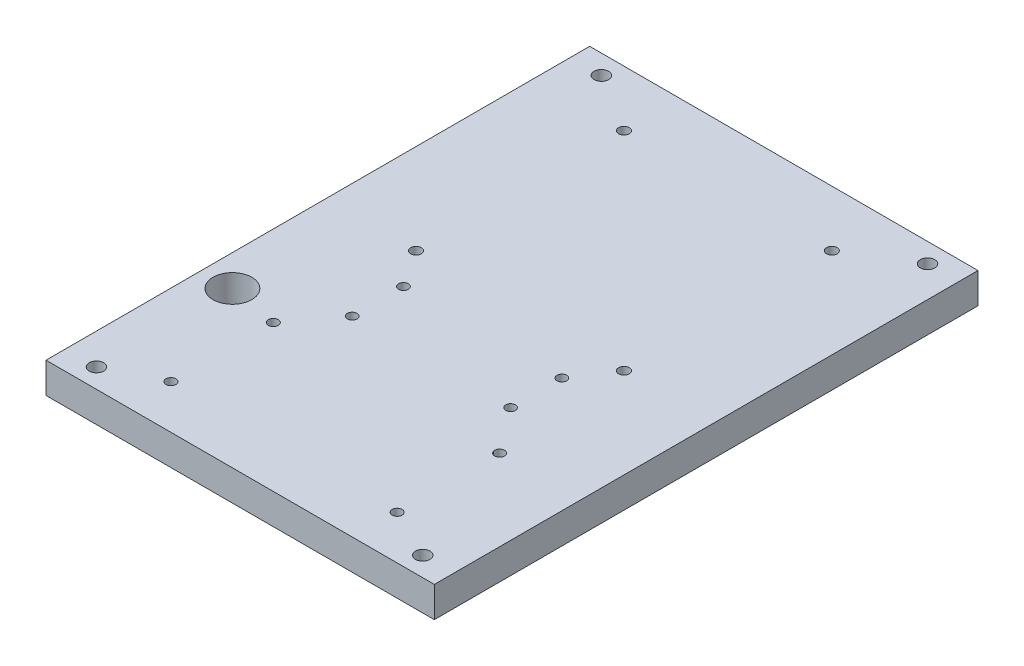
SolidWorks part; units mm, degrees
ref_plane "Front" through (0, 0, 0) normal (0, 0, 1) x (1, 0, 0)
ref_plane "Top" through (0, 0, 0) normal (0, 1, 0) x (1, 0, 0)
ref_plane "Right" through (0, 0, 0) normal (1, 0, 0) x (0, 0, -1)
sketch "Sketch1" plane through (0, 0, 0) normal (0, 1, 0) x (1, 0, 0)
  line L0 (0, -88.9) -> (0, 88.9) construction
  line L1 (63.5, -88.9) -> (-63.5, -88.9)
  line L2 (63.5, -88.9) -> (63.5, 88.9)
  line L3 (63.5, 88.9) -> (-63.5, 88.9)
  line L4 (-63.5, -88.9) -> (-63.5, 88.9)
  line L5 (63.5, -88.9) -> (-63.5, 88.9) construction
  line L6 (63.5, 88.9) -> (-63.5, -88.9) construction
  circle A0 centre (-53.34, 82.55) radius 2.3749
  circle A1 centre (53.34, 82.55) radius 2.3749
  circle A2 centre (53.34, -82.55) radius 2.3749
  circle A3 centre (-53.34, -82.55) radius 2.3749
  circle A4 centre (-53.34, -38.1) radius 6.35
  point P0 (0, 0)
  dimension "D3" = 4.7498
  dimension "D8" = 12.7
  dimension "D1" = 177.8
  dimension "D2" = 127
  dimension "D4" = 53.34
  dimension "D5" = 53.34
  dimension "D6" = 6.35
  dimension "D7" = 6.35
  dimension "D9" = 50.8
  dimension "D10" = 53.34
extrude "Boss-Extrude1" add sketch "Sketch1" along normal blind 10
sketch "sensorbar" plane through (0, 10, 0) normal (0, 1, 0) x (1, 0, 0)
  line L0 (47.625, 77.1685) -> (-47.625, 77.1685) construction
  line L1 (47.625, 77.1685) -> (47.625, 87.8185) construction
  line L2 (47.625, 87.8185) -> (-47.625, 87.8185) construction
  line L3 (-47.625, 77.1685) -> (-47.625, 87.8185) construction
  line L4 (44.875, 81.1685) -> (0, 81.1685) construction
  line L5 (0, 81.1685) -> (-44.875, 81.1685) construction
  circle A0 centre (-44.875, 81.1685) radius 1.75
  circle A1 centre (44.875, 81.1685) radius 1.75
  dimension "D1" = 3.5
  dimension "D2" = 10.65
  dimension "D3" = 95.25
  dimension "D4" = 2.75
  dimension "D5" = 4
  dimension "D6" = 2.75
extrude "senseBar" [suppressed] cut sketch "sensorbar" against normal through all
sketch "Sketch3" plane through (0, 10, 0) normal (0, 1, 0) x (1, 0, 0)
  line L0 (0, 38.2287) -> (-63.5, 38.2287) construction
  line L1 (0, 38.2287) -> (63.5, 38.2287) construction
  line L2 (-63.5, 88.9) -> (-63.5, -88.9) construction
  line L3 (63.5, -88.9) -> (63.5, 88.9) construction
  circle A0 centre (0, 38.2287) radius 1.625
  circle A1 centre (0, -18.1213) radius 1.625
  dimension "D1" = 3.25
  dimension "D2" = 56.35
extrude "battery pack" [suppressed] cut sketch "Sketch3" against normal blind 10
sketch "Sketch4" plane through (0, 10, 0) normal (0, 1, 0) x (1, 0, 0)
  line L0 (-53.7537, 17.5695) -> (-53.7537, 29.5695)
  line L1 (-53.7537, 29.5695) -> (-58.1287, 29.5695)
  line L2 (-58.1287, 29.5695) -> (-58.1287, 35.5695)
  line L3 (-58.1287, 35.5695) -> (-53.7537, 35.5695)
  line L4 (-53.7537, 35.5695) -> (-53.7537, 47.5695)
  line L5 (-53.7537, 47.5695) -> (-48.5037, 47.5695)
  line L6 (-48.5037, 47.5695) -> (-48.5037, 35.5695)
  line L7 (-48.5037, 35.5695) -> (-44.1287, 35.5695)
  line L8 (-44.1287, 35.5695) -> (-44.1287, 29.5695)
  line L9 (-44.1287, 29.5695) -> (-48.5037, 29.5695)
  line L10 (-48.5037, 29.5695) -> (-48.5037, 17.5695)
  line L11 (-48.5037, 17.5695) -> (-53.7537, 17.5695)
  line L12 (0, 88.9) -> (0, -88.9) construction
  line L13 (63.5, 88.9) -> (-63.5, 88.9) construction
  line L14 (-63.5, -88.9) -> (63.5, -88.9) construction
  line L15 (48.5037, 17.5695) -> (53.7537, 17.5695)
  line L16 (48.5037, 29.5695) -> (48.5037, 17.5695)
  line L17 (44.1287, 29.5695) -> (48.5037, 29.5695)
  line L18 (44.1287, 35.5695) -> (44.1287, 29.5695)
  line L19 (48.5037, 35.5695) -> (44.1287, 35.5695)
  line L20 (48.5037, 47.5695) -> (48.5037, 35.5695)
  line L21 (53.7537, 47.5695) -> (48.5037, 47.5695)
  line L22 (53.7537, 35.5695) -> (53.7537, 47.5695)
  line L23 (58.1287, 35.5695) -> (53.7537, 35.5695)
  line L24 (58.1287, 29.5695) -> (58.1287, 35.5695)
  line L25 (53.7537, 29.5695) -> (58.1287, 29.5695)
  line L26 (53.7537, 17.5695) -> (53.7537, 29.5695)
  circle A0 centre (-56.7537, 14.5695) radius 1.625
  circle A1 centre (-56.7537, 6.0695) radius 1.625
  circle A2 centre (56.7537, 6.0695) radius 1.625
  circle A3 centre (56.7537, 14.5695) radius 1.625
  dimension "D8" = 3.25
  dimension "D1" = 5.25
  dimension "D2" = 3
  dimension "D3" = 8.5
  dimension "D4" = 6
  dimension "D5" = 12
  dimension "D6" = 14
  dimension "D7" = 3
extrude "motor Mounts" [suppressed] cut sketch "Sketch4" against normal blind 10
sketch "Sketch5" plane through (0, 10, 0) normal (0, 1, 0) x (1, 0, 0)
  line L1 (-38.533, -68.878) -> (37.827, -68.878) construction
  line L2 (-38.533, -68.878) -> (-38.533, -14.578) construction
  line L3 (-38.533, -14.578) -> (37.827, -14.578) construction
  line L4 (37.827, -68.878) -> (37.827, -14.578) construction
  circle A0 centre (-33.283, -19.828) radius 1.625
  circle A1 centre (32.577, -19.828) radius 1.625
  circle A2 centre (32.577, -63.628) radius 1.625
  circle A3 centre (-33.283, -63.628) radius 1.625
  dimension "D4" = 3.25
  dimension "D6" = 5.25
  dimension "D2" = 54.3
  dimension "D3" = 76.36
  dimension "D5" = 5.25
  dimension "D7" = 5.25
  dimension "D8" = 5.25
extrude "mtr_ctrl" [suppressed] cut sketch "Sketch5" against normal blind 10
sketch "Sketch6" plane through (0, 10, 0) normal (0, 1, 0) x (1, 0, 0)
  line L1 (47.9213, 69.1466) -> (-47.3787, 69.1466) construction
  line L2 (47.9213, 69.1466) -> (47.9213, 18.3366) construction
  line L3 (47.9213, 18.3366) -> (-47.3787, 18.3366) construction
  line L4 (-47.3787, 69.1466) -> (-47.3787, 18.3366) construction
  circle A0 centre (44.6713, 23.3366) radius 1.625
  circle A1 centre (-44.1287, 23.3366) radius 1.625
  circle A2 centre (-44.1287, 64.1466) radius 1.625
  circle A3 centre (44.6713, 64.1466) radius 1.625
  dimension "D7" = 3.25
  dimension "D1" = 95.3
  dimension "D2" = 50.81
  dimension "D3" = 5
  dimension "D4" = 5
  dimension "D5" = 3.25
  dimension "D6" = 3.25
extrude "ang_ctrl" [suppressed] cut sketch "Sketch6" against normal blind 10
sketch "Sketch7" plane through (0, 10, 0) normal (0, 1, 0) x (1, 0, 0)
  line L1 (-15.5, -81.6952) -> (15.5, -81.6952) construction
  line L2 (-15.5, -81.6952) -> (-15.5, -58.1952) construction
  line L3 (-15.5, -58.1952) -> (15.5, -58.1952) construction
  line L4 (15.5, -81.6952) -> (15.5, -58.1952) construction
  line L5 (0, -88.9) -> (0, 88.9) construction
  line L7 (63.5, 88.9) -> (-63.5, 88.9) construction
  line L8 (-63.5, -88.9) -> (63.5, -88.9) construction
  circle A0 centre (-15.5, -58.1952) radius 1.625
  circle A1 centre (15.5, -58.1952) radius 1.625
  circle A2 centre (15.5, -81.6952) radius 1.625
  circle A3 centre (-15.5, -81.6952) radius 1.625
  point P10 (0, -58.1952)
  dimension "D4" = 3.25
  dimension "D1" = 23.5
  dimension "D2" = 31
extrude "front wheel" [suppressed] cut sketch "Sketch7" against normal blind 10 contours A0
sketch "Sketch8" plane through (0, 10, 0) normal (0, 1, 0) x (1, 0, 0)
  line L0 (0, -88.9) -> (0, 88.9) construction
  line L1 (37, -74.5498) -> (-37, -74.5498) construction
  line L2 (37, -74.5498) -> (37, -41.0498) construction
  line L3 (37, -41.0498) -> (-37, -41.0498) construction
  line L4 (-37, -74.5498) -> (-37, -41.0498) construction
  line L7 (37, -57.7998) -> (0, -57.7998) construction
  line L8 (0, -57.7998) -> (-37, -57.7998) construction
  line L13 (63.5, 88.9) -> (-63.5, 88.9) construction
  line L14 (-63.5, -88.9) -> (63.5, -88.9) construction
  line L15 (41.85, -80.3998) -> (-41.85, -80.3998) construction
  line L16 (41.85, -80.3998) -> (41.85, -35.1998) construction
  line L17 (41.85, -35.1998) -> (-41.85, -35.1998) construction
  line L18 (-41.85, -80.3998) -> (-41.85, -35.1998) construction
  line L19 (41.85, -80.3998) -> (-41.85, -35.1998) construction
  line L20 (41.85, -35.1998) -> (-41.85, -80.3998) construction
  circle A0 centre (37, -74.5498) radius 1.625
  circle A1 centre (-37, -74.5498) radius 1.625
  circle A2 centre (-37, -41.0498) radius 1.625
  circle A3 centre (37, -41.0498) radius 1.625
  dimension "D1" = 33.5
  dimension "D2" = 74
  dimension "D3" = 83.7
  dimension "D4" = 45.2
extrude "Breadboard" cut sketch "Sketch8" against normal blind 10
sketch "Sketch9" plane through (0, 10, 0) normal (0, 1, 0) x (1, 0, 0)
  line L1 (38.1, -1.4963) -> (-38.1, -1.4963) construction
  line L2 (38.1, -1.4963) -> (38.1, 74.7037) construction
  line L3 (38.1, 74.7037) -> (-38.1, 74.7037) construction
  line L4 (-38.1, -1.4963) -> (-38.1, 74.7037) construction
  line L5 (38.1, -1.4963) -> (-38.1, 74.7037) construction
  line L6 (38.1, 74.7037) -> (-38.1, -1.4963) construction
  line L7 (34, 2.6037) -> (-34, 2.6037) construction
  line L8 (34, 2.6037) -> (34, 70.6037) construction
  line L9 (34, 70.6037) -> (-34, 70.6037) construction
  line L10 (-34, 2.6037) -> (-34, 70.6037) construction
  line L11 (34, 2.6037) -> (-34, 70.6037) construction
  line L12 (34, 70.6037) -> (-34, 2.6037) construction
  line L14 (0, 88.9) -> (0, -88.9) construction
  circle A0 centre (-34, 70.6037) radius 1.75
  circle A1 centre (34, 70.6037) radius 1.75
  circle A2 centre (34, 2.6037) radius 1.75
  circle A3 centre (-34, 2.6037) radius 1.75
  point P0 (0, 36.6037)
  point P5 (0, 36.6037)
  dimension "D3" = 3.5
  dimension "D1" = 76.2
  dimension "D2" = 76.2
  dimension "D4" = 68
extrude "FPGA" cut sketch "Sketch9" against normal blind 10
sketch "Sketch10" plane through (0, 10, 0) normal (0, 1, 0) x (1, 0, 0)
  line L0 (-70.4036, -17.9757) -> (70.4036, -17.9757) construction
  line L1 (0, 30.8882) -> (0, -66.8396) construction
  line L2 (-28.575, -6.4187) -> (28.575, -6.4187)
  line L3 (-28.575, -6.4187) -> (-28.575, -29.5327)
  line L4 (-28.575, -29.5327) -> (28.575, -29.5327)
  line L5 (28.575, -6.4187) -> (28.575, -29.5327)
  circle A0 centre (-25.908, -9.5937) radius 1.5875
  circle A1 centre (25.908, -9.5937) radius 1.5875
  circle A2 centre (25.908, -26.3577) radius 1.5875
  circle A3 centre (-25.908, -26.3577) radius 1.5875
  point P12 (0, -17.9757)
  point P17 (0, -6.4187)
  point P18 (28.575, -17.9757)
  dimension "D1" = 3.175
  dimension "D2" = 3.175
  dimension "D3" = 3.175
  dimension "D4" = 3.175
  dimension "D5" = 57.15
  dimension "D6" = 23.114
  dimension "D7" = 25.908
  dimension "D8" = 25.908
  dimension "D9" = 25.908
  dimension "D10" = 25.908
  dimension "D11" = 8.382
  dimension "D12" = 8.382
  dimension "D13" = 8.382
  dimension "D14" = 8.382
extrude "8Push_btn" cut sketch "Sketch10" against normal blind 10 contours A0 | A3 | A2 | A1
